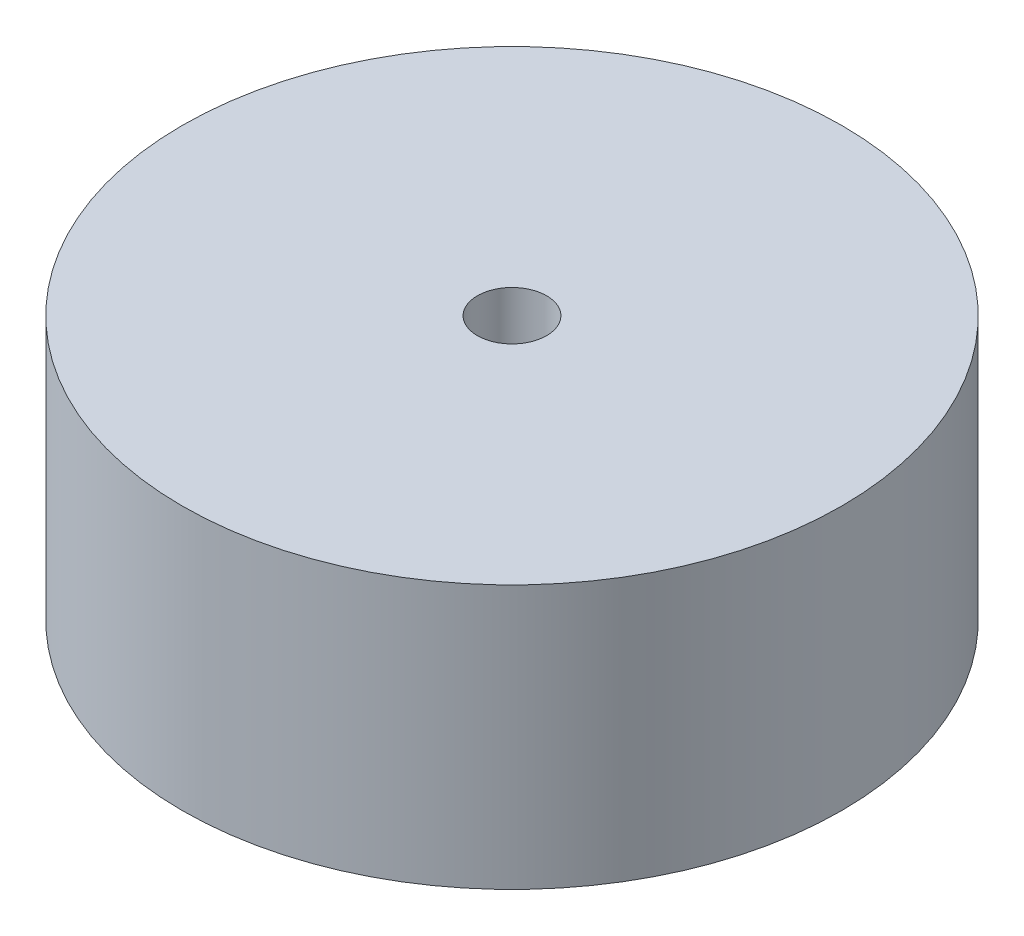
SolidWorks part; units mm, degrees
ref_plane "Front Plane" through (0, 0, 0) normal (0, 0, 1) x (1, 0, 0)
ref_plane "Top Plane" through (0, 0, 0) normal (0, 1, 0) x (1, 0, 0)
ref_plane "Right Plane" through (0, 0, 0) normal (1, 0, 0) x (0, 0, -1)
sketch "Sketch1" plane through (0, 0, 0) normal (0, 1, 0) x (1, 0, 0)
  circle A0 centre (0, 0) radius 10
  circle A1 centre (0, 0) radius 1.05
  dimension "D1" = 20
  dimension "D2" = 2.1
extrude "Boss-Extrude1" add sketch "Sketch1" along normal blind 8
sketch "Sketch2" plane through (0, 8, 0) normal (0, 1, 0) x (1, 0, 0)
  circle A0 centre (0, 0) radius 7.5
  dimension "D1" = 15
